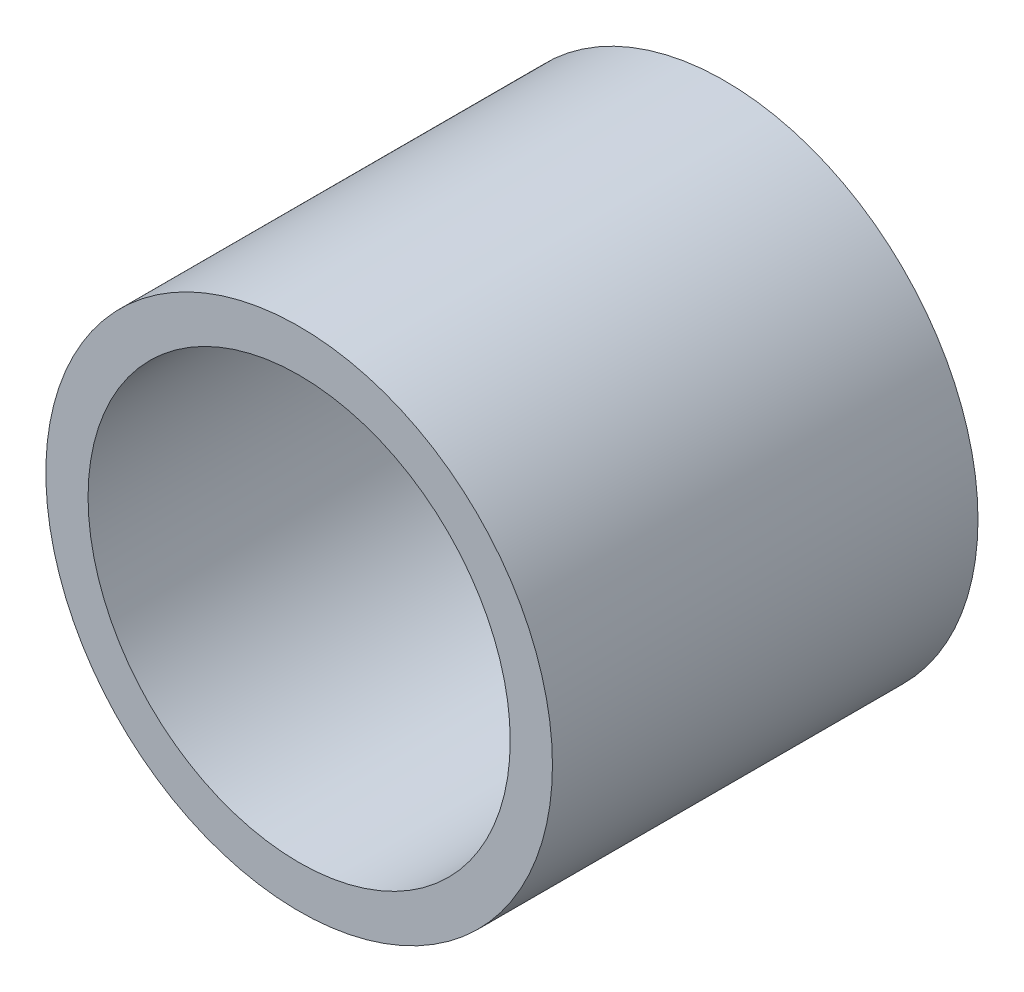
SolidWorks part; units mm, degrees
material "Plain Carbon Steel"
ref_plane "Front Plane" through (0, 0, 0) normal (0, 0, 1) x (1, 0, 0)
ref_plane "Top Plane" through (0, 0, 0) normal (0, 1, 0) x (1, 0, 0)
ref_plane "Right Plane" through (0, 0, 0) normal (1, 0, 0) x (0, 0, -1)
sketch "Sketch1" plane through (0, 0, 0) normal (0, 0, 1) x (1, 0, 0)
  circle A0 centre (0, 0) radius 9.525
  circle A1 centre (0, 0) radius 7.9375
  dimension "D1" = 19.05
  dimension "D2" = 15.875
extrude "Boss-Extrude1" add sketch "Sketch1" along normal mid plane 16.002
